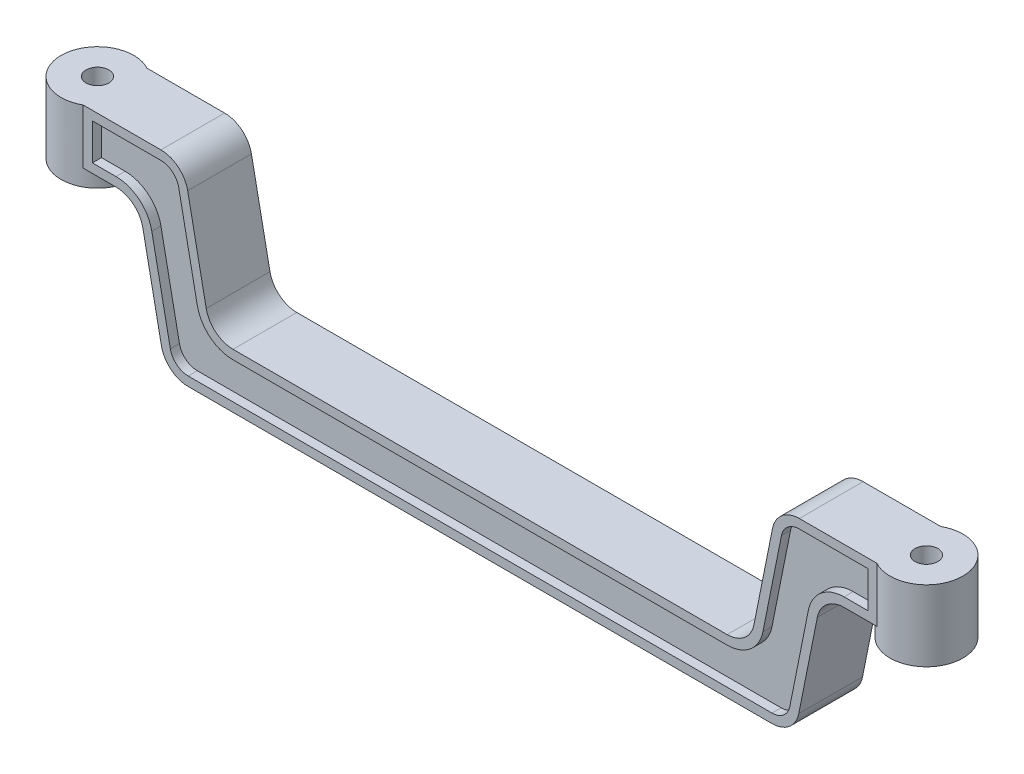
SolidWorks part; units mm, degrees
ref_plane "Front Plane" through (0, 0, 0) normal (0, 0, 1) x (1, 0, 0)
ref_plane "Top Plane" through (0, 0, 0) normal (0, 1, 0) x (1, 0, 0)
ref_plane "Right Plane" through (0, 0, 0) normal (1, 0, 0) x (0, 0, -1)
sketch "Sketch1" plane through (0, 0, 0) normal (0, 0, 1) x (1, 0, 0)
  line L0 (-34.5, 0) -> (34.5, 0)
  line L2 (37.5, 15) -> (45.5, 15)
  line L3 (0, 35.5654) -> (0, -30.8762) construction
  line L4 (-37.5, 15) -> (-45.5, 15)
  line L6 (34.5, 21) -> (45.5, 21)
  line L8 (-29.5812, 6) -> (29.5812, 6)
  line L10 (-32.5812, 21) -> (-45.5, 21)
  line L11 (45.5, 15) -> (45.5, 21)
  line L12 (-45.5, 15) -> (-45.5, 21)
  line L13 (31.5, 21) -> (45.5, 21) construction
  line L14 (31.5, 6) -> (31.5, 21) construction
  line L15 (-37.5, 0) -> (37.5, 0) construction
  line L16 (37.5, 0) -> (37.5, 15) construction
  line L17 (-31.5, 6) -> (-31.5, 21) construction
  line L18 (-31.5, 21) -> (-45.5, 21) construction
  line L19 (-37.5, 0) -> (-37.5, 15) construction
  line L20 (-37.5, 15) -> (-34.5, 0)
  line L22 (37.5, 15) -> (34.5, 0)
  line L23 (-31.5, 6) -> (31.5, 6) construction
  line L24 (-32.5812, 21) -> (-29.5812, 6)
  line L26 (32.5812, 21) -> (29.5812, 6)
  line L27 (32.5812, 21) -> (34.5, 21)
  point P21 (37.5, 0)
  point P28 (-31.6165, 16.1767)
  point P29 (-28.6165, 1.1767)
  dimension "D6" = 6
  dimension "D1" = 91
  dimension "D2" = 37.5
  dimension "D3" = 8
  dimension "D4" = 15
  dimension "D5" = 6
extrude "Boss-Extrude2" add sketch "Sketch1" along normal blind 7
sketch "Sketch2" plane through (0, 21, 0) normal (0, 1, 0) x (1, 0, 0)
  line L0 (45.5, -7) -> (45.5, 0) construction
  circle A0 centre (45.5, -3.5) radius 4
  dimension "D1" = 8
extrude "Boss-Extrude3" add sketch "Sketch2" against normal blind 7.8
mirror "Mirror1" about plane through (0, 0, 0) normal (1, 0, 0) of "Boss-Extrude3"
sketch "Sketch3" plane through (0, 21, 0) normal (0, 1, 0) x (1, 0, 0)
  line L0 (45.5, 0.5) -> (45.5, -7.5) construction
  line L1 (49.5, -3.5) -> (41.8426, -3.5) construction
  arc A0 (43.5635, -7) -> (43.5635, 0) centre (45.5, -3.5) ccw construction
  circle A1 centre (45.5, -3.5) radius 1.25
  dimension "D1" = 2.5
extrude "Cut-Extrude1" cut sketch "Sketch3" against normal up to surface (7.8 mm away) up to face at (45.5, 13.2, 7.5)
mirror "Mirror2" about plane through (0, 0, 0) normal (1, 0, 0) of "Cut-Extrude1"
fillet "Fillet1" radius 3 2 edges at (29.5812, 6, 3.5) (34.5, 0, 3.5)
fillet "Fillet2" radius 3 6 edges at (37.5, 15, 3.5) (-37.5, 15, 3.5) (-34.5, 0, 3.5) (-29.5812, 6, 3.5) (-32.5812, 21, 3.5) (32.5812, 21, 3.5)
sketch "Sketch4" plane through (0, 0, 7) normal (0, 0, 1) x (1, 0, 0)
  line L24 (-36.0371, 12.7845) -> (-34.0017, 2.6078)
  line L25 (-32.0406, 1) -> (32.0406, 1)
  line L26 (34.0017, 2.6078) -> (36.0371, 12.7845)
  line L27 (39.9594, 16) -> (42.5635, 16)
  line L28 (42.5635, 16) -> (42.5635, 20)
  line L29 (42.5635, 20) -> (35.0406, 20)
  line L30 (33.0794, 18.3922) -> (31.0441, 8.2155)
  line L31 (27.1218, 5) -> (-27.1218, 5)
  line L32 (-31.0441, 8.2155) -> (-33.0794, 18.3922)
  line L33 (-35.0406, 20) -> (-42.5635, 20)
  line L34 (-42.5635, 20) -> (-42.5635, 16)
  line L35 (-42.5635, 16) -> (-39.9594, 16)
  line L36 (-36.0371, 12.7845) -> (-34.0017, 2.6078)
  line L37 (-32.0406, 1) -> (32.0406, 1)
  line L38 (34.0017, 2.6078) -> (36.0371, 12.7845)
  line L39 (39.9594, 16) -> (42.5635, 16)
  line L40 (42.5635, 16) -> (42.5635, 20)
  line L41 (42.5635, 20) -> (35.0406, 20)
  line L42 (33.0794, 18.3922) -> (31.0441, 8.2155)
  line L43 (27.1218, 5) -> (-27.1218, 5)
  line L44 (-31.0441, 8.2155) -> (-33.0794, 18.3922)
  line L45 (-35.0406, 20) -> (-42.5635, 20)
  line L46 (-42.5635, 20) -> (-42.5635, 16)
  line L47 (-42.5635, 16) -> (-39.9594, 16)
  arc A16 (-34.0017, 2.6078) -> (-32.0406, 1) centre (-32.0406, 3) ccw
  arc A17 (32.0406, 1) -> (34.0017, 2.6078) centre (32.0406, 3) ccw
  arc A18 (39.9594, 16) -> (36.0371, 12.7845) centre (39.9594, 12) ccw
  arc A19 (35.0406, 20) -> (33.0794, 18.3922) centre (35.0406, 18) ccw
  arc A20 (27.1218, 5) -> (31.0441, 8.2155) centre (27.1218, 9) ccw
  arc A21 (-31.0441, 8.2155) -> (-27.1218, 5) centre (-27.1218, 9) ccw
  arc A22 (-33.0794, 18.3922) -> (-35.0406, 20) centre (-35.0406, 18) ccw
  arc A23 (-36.0371, 12.7845) -> (-39.9594, 16) centre (-39.9594, 12) ccw
  arc A24 (-34.0017, 2.6078) -> (-32.0406, 1) centre (-32.0406, 3) ccw
  arc A25 (32.0406, 1) -> (34.0017, 2.6078) centre (32.0406, 3) ccw
  arc A26 (39.9594, 16) -> (36.0371, 12.7845) centre (39.9594, 12) ccw
  arc A27 (35.0406, 20) -> (33.0794, 18.3922) centre (35.0406, 18) ccw
  arc A28 (27.1218, 5) -> (31.0441, 8.2155) centre (27.1218, 9) ccw
  arc A29 (-31.0441, 8.2155) -> (-27.1218, 5) centre (-27.1218, 9) ccw
  arc A30 (-33.0794, 18.3922) -> (-35.0406, 20) centre (-35.0406, 18) ccw
  arc A31 (-36.0371, 12.7845) -> (-39.9594, 16) centre (-39.9594, 12) ccw
  dimension "D1" = 1
extrude "Cut-Extrude2" cut sketch "Sketch4" against normal blind 1
